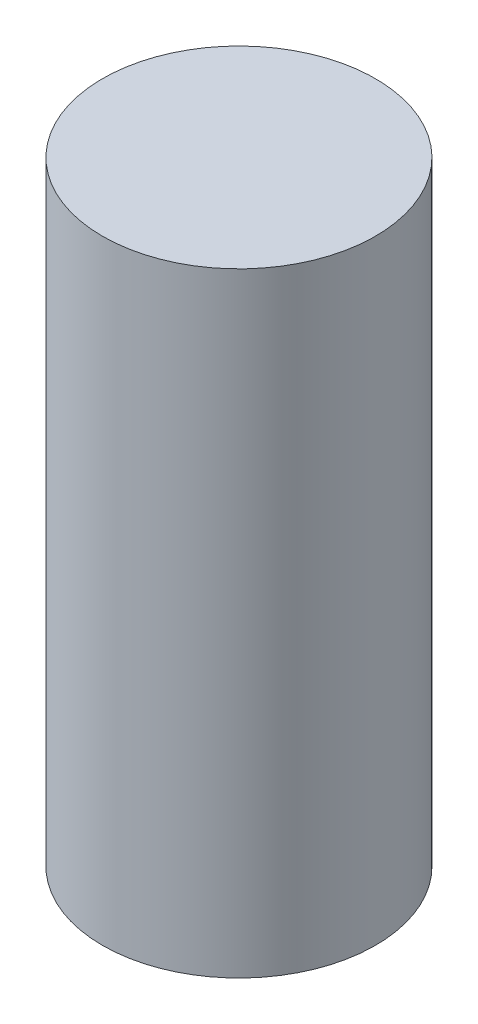
SolidWorks part; units mm, degrees
ref_plane "Front Plane" through (0, 0, 0) normal (0, 0, 1) x (1, 0, 0)
ref_plane "Top Plane" through (0, 0, 0) normal (0, 1, 0) x (1, 0, 0)
ref_plane "Right Plane" through (0, 0, 0) normal (1, 0, 0) x (0, 0, -1)
sketch "Sketch1" plane through (0, 0, 0) normal (0, 1, 0) x (1, 0, 0)
  circle A0 centre (0, 0) radius 10
  dimension "D1" = 20
extrude "Boss-Extrude1" add sketch "Sketch1" along normal blind 45
